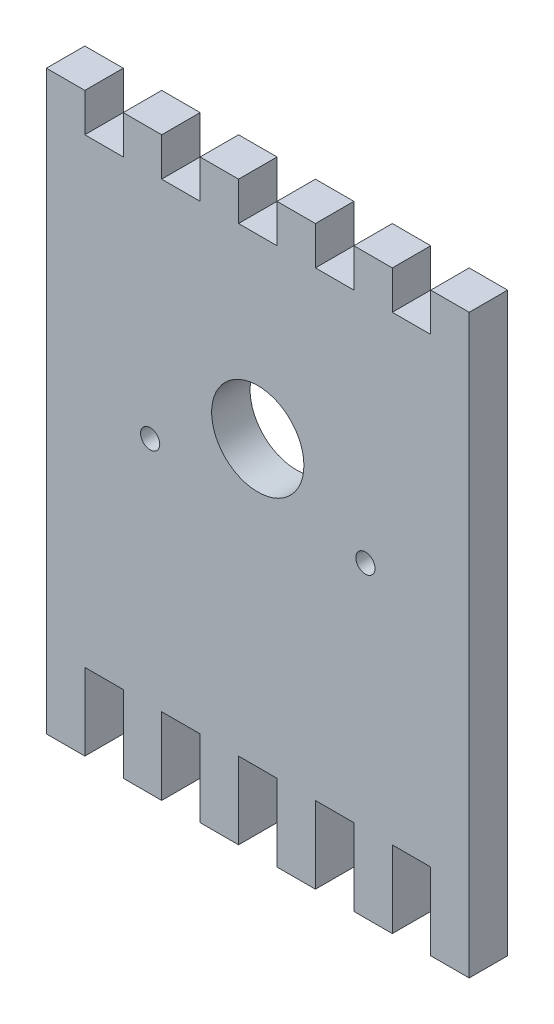
SolidWorks part; units mm, degrees
ref_plane "Plan de face" through (0, 0, 0) normal (0, 0, 1) x (1, 0, 0)
ref_plane "Plan de dessus" through (0, 0, 0) normal (0, 1, 0) x (1, 0, 0)
ref_plane "Plan de droite" through (0, 0, 0) normal (1, 0, 0) x (0, 0, -1)
sketch "Esquisse1" plane through (0, 0, 0) normal (0, 0, 1) x (1, 0, 0)
  line L0 (10, 65) -> (15, 65)
  line L1 (0, 0) -> (55, 0)
  line L2 (0, 0) -> (0, 60)
  line L3 (0, 60) -> (55, 60)
  line L4 (55, 0) -> (55, 60)
  line L5 (0, 60) -> (5, 60)
  line L6 (0, 60) -> (0, 65)
  line L7 (0, 65) -> (5, 65)
  line L8 (5, 60) -> (5, 65)
  line L9 (15, 60) -> (15, 65)
  line L10 (10, 60) -> (10, 65)
  line L11 (20, 65) -> (25, 65)
  line L12 (25, 60) -> (25, 65)
  line L13 (20, 60) -> (20, 65)
  line L14 (30, 65) -> (35, 65)
  line L15 (35, 60) -> (35, 65)
  line L16 (30, 60) -> (30, 65)
  line L17 (40, 65) -> (45, 65)
  line L18 (45, 60) -> (45, 65)
  line L19 (40, 60) -> (40, 65)
  line L20 (50, 65) -> (55, 65)
  line L21 (55, 60) -> (55, 65)
  line L22 (50, 60) -> (50, 65)
  line L23 (15, 0) -> (15, -10)
  line L24 (0, 0) -> (5, 0)
  line L25 (0, 0) -> (0, -10)
  line L26 (0, -10) -> (5, -10)
  line L27 (5, 0) -> (5, -10)
  line L28 (10, 0) -> (10, -10)
  line L29 (10, -10) -> (15, -10)
  line L30 (25, 0) -> (25, -10)
  line L31 (20, 0) -> (20, -10)
  line L32 (20, -10) -> (25, -10)
  line L33 (35, 0) -> (35, -10)
  line L34 (30, 0) -> (30, -10)
  line L35 (30, -10) -> (35, -10)
  line L36 (45, 0) -> (45, -10)
  line L37 (40, 0) -> (40, -10)
  line L38 (40, -10) -> (45, -10)
  line L39 (55, 0) -> (55, -10)
  line L40 (50, 0) -> (50, -10)
  line L41 (50, -10) -> (55, -10)
  circle A0 centre (27.5, 30) radius 17
  circle A1 centre (27.5, 37) radius 6
  circle A2 centre (13.5, 30) radius 1.25
  circle A3 centre (41.5, 30) radius 1.25
  dimension "D3" = 34
  dimension "D13" = 12
  dimension "D14" = 2.5
  dimension "D15" = 2.5
  dimension "D1" = 60
  dimension "D2" = 55
  dimension "D4" = 27.5
  dimension "D5" = 30
  dimension "D6" = 5
  dimension "D7" = 5
  dimension "D9" = 5
  dimension "D10" = 10
  dimension "D12" = 7
  dimension "D16" = 14
  dimension "D17" = 14
  dimension "D18" = 7
  dimension "D8" = 6
  dimension "D11" = 6
extrude "Boss.-Extru.1" add sketch "Esquisse1" along normal blind 5 contours L1 L4 L3 L2 A0 | A0 A3 A2 A1 | L27 L1 L25 L26 | L28 L29 L23 L1 | L31 L32 L30 L1 | L34 L35 L33 L1 | L37 L38 L36 L1 | L40 L41 L39 L1 | L3 L8 L7 L6 | L13 L3 L12 L11 | L10 L3 L9 L0 | L16 L3 L15 L14 | L19 L3 L18 L17 | L22 L3 L21 L20
